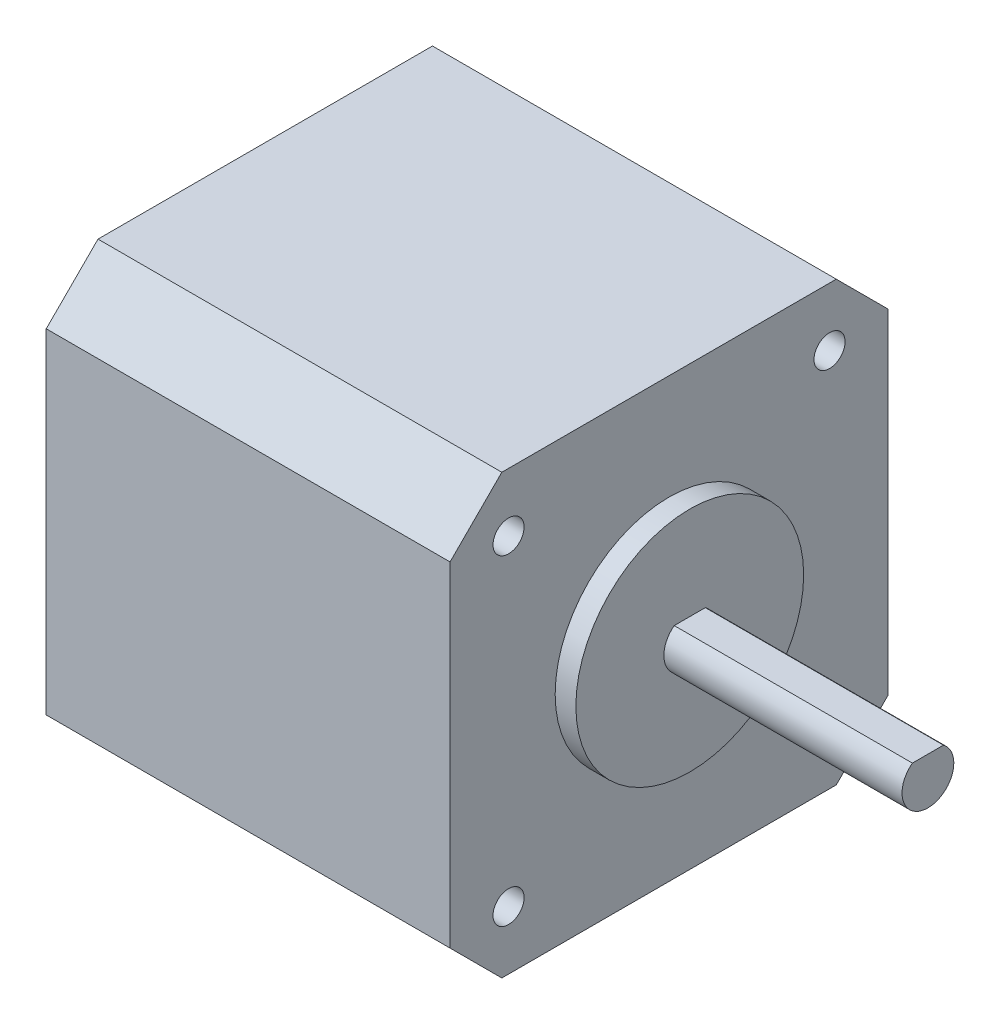
SolidWorks part; units mm, degrees
ref_plane "Front Plane" through (0, 0, 0) normal (0, 0, 1) x (1, 0, 0)
ref_plane "Top Plane" through (0, 0, 0) normal (0, 1, 0) x (1, 0, 0)
ref_plane "Right Plane" through (0, 0, 0) normal (1, 0, 0) x (0, 0, -1)
sketch "Sketch1" plane through (0, 0, 0) normal (1, 0, 0) x (0, 0, -1)
  line L0 (0, 37.3) -> (5, 42.3)
  line L1 (5, 0) -> (37.3, 0)
  line L2 (0, 5) -> (0, 37.3)
  line L3 (5, 42.3) -> (37.3, 42.3)
  line L4 (42.3, 5) -> (42.3, 37.3)
  line L5 (0, 0) -> (42.3, 42.3) construction
  line L6 (0, 42.3) -> (42.3, 0) construction
  line L7 (0, 5) -> (5, 0)
  line L8 (37.3, 0) -> (42.3, 5)
  line L9 (42.3, 37.3) -> (37.3, 42.3)
  circle A0 centre (5.65, 36.65) radius 1.5
  circle A1 centre (36.65, 36.65) radius 1.5
  circle A2 centre (36.65, 5.65) radius 1.5
  circle A3 centre (5.65, 5.65) radius 1.5
  point P4 (21.15, 21.15)
  dimension "D4" = 3
  dimension "D1" = 42.3
  dimension "D2" = 42.3
  dimension "D3" = 31
extrude "Boss-Extrude1" add sketch "Sketch1" along normal blind 39 contours L1 L4 L3 L2 A3 A2 A1 A0
sketch "Sketch2" plane through (39, 0, 0) normal (1, 0, 0) x (0, 0, -1)
  line L0 (0, 21.15) -> (42.3, 21.15) construction
  line L1 (0, 5) -> (0, 37.3) construction
  line L2 (42.3, 5) -> (42.3, 37.3) construction
  line L3 (21.15, 42.3) -> (21.15, 0) construction
  line L4 (5, 42.3) -> (37.3, 42.3) construction
  line L5 (5, 0) -> (37.3, 0) construction
  circle A0 centre (21.15, 21.15) radius 11
  point P12 (21.15, 42.3)
  dimension "D1" = 22
extrude "Boss-Extrude2" add sketch "Sketch2" along normal blind 2 contours A0
sketch "Sketch3" plane through (41, 0, 0) normal (1, 0, 0) x (0, 0, -1)
  line L0 (19.65, 23.15) -> (22.65, 23.15)
  arc A0 (19.65, 23.15) -> (22.65, 23.15) centre (21.15, 21.15) ccw
  circle A1 centre (21.15, 21.15) radius 11
  circle A2 centre (21.15, 21.15) radius 11 construction
  point P6 (21.15, 18.65)
  dimension "D2" = 5
  dimension "D3" = 4.5
  dimension "D1" = 0
extrude "Boss-Extrude3" add sketch "Sketch3" along normal blind 23 contours A0 L0
